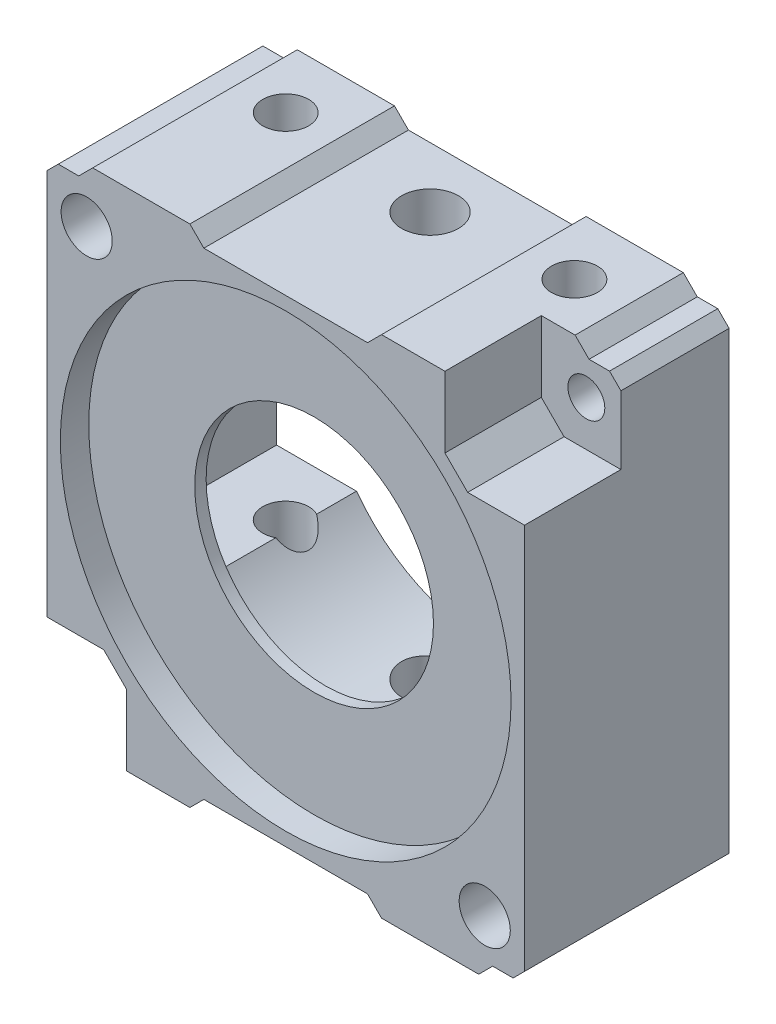
SolidWorks part; units mm, degrees
ref_plane "Front Plane" through (0, 0, 0) normal (0, 0, 1) x (1, 0, 0)
ref_plane "Top Plane" through (0, 0, 0) normal (0, 1, 0) x (1, 0, 0)
ref_plane "Right Plane" through (0, 0, 0) normal (1, 0, 0) x (0, 0, -1)
sketch "Sketch1" plane through (0, 0, 0) normal (0, 0, 1) x (1, 0, 0)
  line L0 (0, 0) -> (0, 21) construction
  line L1 (-7.2, 21) -> (7.2, 21)
  line L2 (7.2, 21) -> (8.43, 21) construction
  line L3 (8.43, 21) -> (8.43, 22.23) construction
  line L4 (8.43, 22.23) -> (16.98, 22.23)
  line L5 (7.2, 21) -> (8.43, 22.23)
  line L6 (16.98, 22.23) -> (16.98, 21) construction
  line L7 (16.98, 21) -> (18.21, 21) construction
  line L9 (16.98, 22.23) -> (18.21, 21)
  line L10 (18.21, 21) -> (20.01, 21)
  line L11 (20.01, 21) -> (20.01, 20) construction
  line L12 (20.01, 20) -> (21.01, 20) construction
  line L13 (20.01, 21) -> (21.01, 20)
  line L14 (21.01, 20) -> (21.01, -20)
  line L15 (0, 0) -> (21, 0) construction
  line L16 (20.01, -20) -> (21.01, -20) construction
  line L17 (20.01, -21) -> (20.01, -20) construction
  line L18 (16.98, -21) -> (18.21, -21) construction
  line L19 (16.98, -22.23) -> (16.98, -21) construction
  line L20 (8.43, -21) -> (8.43, -22.23) construction
  line L21 (7.2, -21) -> (8.43, -21) construction
  line L22 (20.01, -21) -> (21.01, -20)
  line L23 (18.21, -21) -> (20.01, -21)
  line L24 (16.98, -22.23) -> (18.21, -21)
  line L25 (7.2, -21) -> (8.43, -22.23)
  line L26 (8.43, -22.23) -> (16.98, -22.23)
  line L27 (-7.2, -21) -> (7.2, -21)
  line L28 (-20.01, 20) -> (-21.01, 20) construction
  line L29 (-20.01, 21) -> (-20.01, 20) construction
  line L30 (-16.98, 21) -> (-18.21, 21) construction
  line L31 (-16.98, 22.23) -> (-16.98, 21) construction
  line L32 (-8.43, 21) -> (-8.43, 22.23) construction
  line L33 (-7.2, 21) -> (-8.43, 21) construction
  line L34 (-21.01, 20) -> (-21.01, -20)
  line L35 (-20.01, 21) -> (-21.01, 20)
  line L36 (-18.21, 21) -> (-20.01, 21)
  line L37 (-16.98, 22.23) -> (-18.21, 21)
  line L38 (-7.2, 21) -> (-8.43, 22.23)
  line L39 (-8.43, 22.23) -> (-16.98, 22.23)
  line L40 (-7.2, -21) -> (-8.43, -21) construction
  line L41 (-8.43, -21) -> (-8.43, -22.23) construction
  line L42 (-16.98, -22.23) -> (-16.98, -21) construction
  line L43 (-16.98, -21) -> (-18.21, -21) construction
  line L44 (-20.01, -21) -> (-20.01, -20) construction
  line L45 (-20.01, -20) -> (-21.01, -20) construction
  line L46 (-8.43, -22.23) -> (-16.98, -22.23)
  line L47 (-7.2, -21) -> (-8.43, -22.23)
  line L48 (-16.98, -22.23) -> (-18.21, -21)
  line L49 (-18.21, -21) -> (-20.01, -21)
  line L50 (-20.01, -21) -> (-21.01, -20)
  point P23 (21.01, 0)
  point P42 (0, -21)
  dimension "D1" = 21
  dimension "D2" = 7.2
  dimension "D3" = 1.23
  dimension "D4" = 1.23
  dimension "D5" = 8.55
  dimension "D6" = 1.23
  dimension "D7" = 1.8
  dimension "D8" = 1
  dimension "D9" = 1
  dimension "D10" = 20
  dimension "D11" = 21
extrude "Boss-Extrude2" add sketch "Sketch1" along normal blind 18 contours L14 L22 L23 L24 L26 L25 L27 L47 L46 L48 L49 L50 L34 L35 L36 L37 L39 L38 L1 L5 L4 L9 L10 L13
sketch "Sketch2" plane through (0, 0, 18) normal (0, 0, 1) x (1, 0, 0)
  circle A0 centre (0, 0) radius 19.825
  dimension "D1" = 39.65
extrude "Cut-Extrude1" cut sketch "Sketch2" against normal blind 2.5
sketch "Sketch3" plane through (0, 0, 0) normal (0, 0, -1) x (-1, 0, 0)
  circle A0 centre (0, 0) radius 14.7
  dimension "D1" = 29.4
extrude "Cut-Extrude2" cut sketch "Sketch3" against normal blind 14.5
sketch "Sketch4" plane through (0, 0, 0) normal (0, 0, -1) x (-1, 0, 0)
  line L0 (0, 0) -> (18.8, 0) construction
  line L1 (18.8, 0) -> (18.8, 8.8)
  line L2 (18.8, 8.8) -> (-18.8, 8.8)
  line L3 (18.8, 0) -> (18.8, -8.8)
  line L4 (18.8, -8.8) -> (-18.8, -8.8)
  line L5 (-18.8, -8.8) -> (-18.8, 8.8)
  dimension "D1" = 18.8
  dimension "D2" = 8.8
  dimension "D3" = 37.6
  dimension "D4" = 8.8
extrude "Cut-Extrude3" cut sketch "Sketch4" against normal blind 14.5
sketch "Sketch5" plane through (0, 0, 14.5) normal (0, 0, -1) x (-1, 0, 0)
  circle A0 centre (0, 0) radius 10.5
  dimension "D1" = 21
extrude "Cut-Extrude4" cut sketch "Sketch5" against normal blind 14.5
sketch "Sketch7" plane through (0, 21, 0) normal (0, 1, 0) x (1, 0, 0)
  line L0 (0, 0) -> (0, -5.3) construction
  line L1 (0, -5.3) -> (12.7, -5.3) construction
  circle A0 centre (0, -5.3) radius 2.5
  circle A1 centre (12.7, -5.3) radius 2.02
  circle A2 centre (-12.7, -5.3) radius 2.02
  dimension "D2" = 5
  dimension "D4" = 4.04
  dimension "D1" = 5.3
  dimension "D3" = 12.7
extrude "Cut-Extrude6" cut sketch "Sketch7" against normal blind 60 and the other way blind 30
sketch "Sketch9" plane through (0, 0, 18) normal (0, 0, 1) x (1, 0, 0)
  line L0 (17.97, 22.23) -> (17.97, 17.97) construction
  line L1 (8.43, 22.23) -> (16.98, 22.23) construction
  line L2 (17.97, 17.97) -> (21.01, 17.97) construction
  line L3 (21.01, 20) -> (21.01, -20) construction
  line L4 (-17.51, 17.505) -> (-21.01, 17.505) construction
  line L6 (-17.51, 22.23) -> (-17.51, 17.505) construction
  line L7 (-16.98, 22.23) -> (-17.51, 22.23) construction
  line L8 (-21.01, 20) -> (-21.01, -20) construction
  line L9 (0, 0) -> (4.242, 4.2432) construction
  line L10 (21.01, -17.505) -> (17.51, -17.505) construction
  line L11 (17.51, -17.505) -> (17.51, -22.23) construction
  line L12 (0, 0) -> (-4.2426, 4.2426) construction
  line L13 (-17.97, -17.97) -> (-17.97, -22.23) construction
  line L14 (-17.97, -17.97) -> (-21.01, -17.97) construction
  circle A0 centre (17.97, 17.97) radius 1.6239
  circle A1 centre (-17.51, 17.505) radius 2.25
  circle A2 centre (17.51, -17.505) radius 2.25
  circle A3 centre (-17.97, -17.97) radius 1.6239
  dimension "D5" = 4.5
  dimension "D1" = 4.26
  dimension "D2" = 3.04
  dimension "D3" = 3.5
  dimension "D4" = 4.725
  dimension "D6" = 6
  dimension "D7" = 3.5
  dimension "D8" = 6
  dimension "D9" = 4.725
  dimension "D10" = 3.04
  dimension "D11" = 4.26
extrude "Cut-Extrude7" cut sketch "Sketch9" against normal blind 30
sketch "Sketch10" plane through (0, 0, 18) normal (0, 0, 1) x (1, 0, 0)
  line L0 (14.01, 22.23) -> (14.01, 16)
  line L1 (8.43, 22.23) -> (16.98, 22.23) construction
  line L2 (14.01, 16) -> (16.01, 14)
  line L4 (16.01, 14) -> (21.01, 14)
  line L5 (21.01, 20) -> (21.01, -20) construction
  line L6 (21.01, 14) -> (21.01, 20)
  line L7 (21.01, 20) -> (20.01, 21)
  line L8 (20.01, 21) -> (18.21, 21)
  line L9 (18.21, 21) -> (16.98, 22.23)
  line L10 (16.98, 22.23) -> (14.01, 22.23)
  line L11 (0, 0) -> (-7.0711, 7.0711) construction
  line L12 (0, 0) -> (7.0711, -7.0711) construction
  line L13 (-21.01, -14) -> (-16.01, -14)
  line L14 (-21.01, 20) -> (-21.01, -20) construction
  line L15 (-16.01, -14) -> (-14.01, -16)
  line L16 (-14.01, -16) -> (-14.01, -22.23)
  line L17 (-8.43, -22.23) -> (-16.98, -22.23) construction
  line L18 (-14.01, -22.23) -> (-16.98, -22.23)
  line L19 (-16.98, -22.23) -> (-18.21, -21)
  line L20 (-18.21, -21) -> (-20.01, -21)
  line L21 (-20.01, -21) -> (-21.01, -20)
  line L22 (-21.01, -20) -> (-21.01, -14)
  dimension "D1" = 6.23
  dimension "D2" = 5
  dimension "D3" = 2
  dimension "D4" = 2
  dimension "D5" = 6.23
  dimension "D6" = 5
  dimension "D7" = 2
  dimension "D8" = 2
extrude "Cut-Extrude8" cut sketch "Sketch10" against normal blind 8.48
